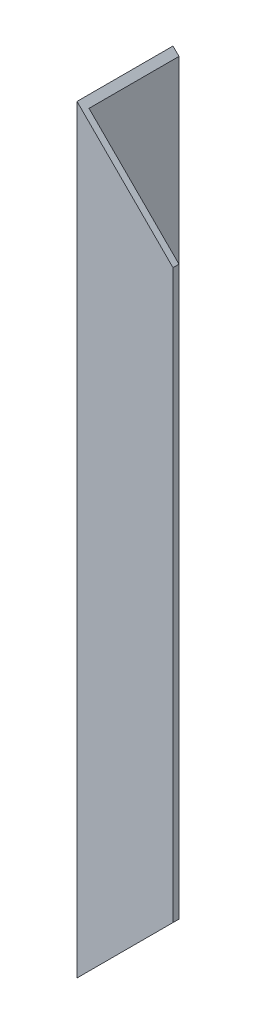
SolidWorks part; units mm, degrees
ref_plane "Front Plane" through (0, 0, 0) normal (0, 0, 1) x (1, 0, 0)
ref_plane "Top Plane" through (0, 0, 0) normal (0, 1, 0) x (1, 0, 0)
ref_plane "Right Plane" through (0, 0, 0) normal (1, 0, 0) x (0, 0, -1)
sketch "Sketch2" plane through (0, 0, 0) normal (0, 1, 0) x (1, 0, 0)
  line L0 (0, 0) -> (0, 25.4)
  line L1 (0, 25.4) -> (1.5875, 25.4)
  line L2 (1.5875, 25.4) -> (1.5875, 1.5875)
  line L3 (1.5875, 1.5875) -> (25.4, 1.5875)
  line L4 (25.4, 1.5875) -> (25.4, 0)
  line L5 (25.4, 0) -> (0, 0)
  dimension "D1" = 25.4
  dimension "D2" = 1.5875
extrude "Boss-Extrude2" add sketch "Sketch2" along normal blind 200.914
sketch "Sketch4" plane through (0, 0, 0) normal (0, 0, 1) x (1, 0, 0)
  line L0 (0, 200.914) -> (25.4, 175.514)
  line L1 (25.4, 200.914) -> (25.4, 0) construction
  line L2 (25.4, 175.514) -> (25.4, 200.914)
  line L3 (25.4, 200.914) -> (0, 200.914)
  dimension "D1" = 45
extrude "Cut-Extrude1" cut sketch "Sketch4" against normal through all
sketch "Sketch5" plane through (0, 0, 0) normal (0, 0, 1) x (1, 0, 0)
  line L0 (0, 0) -> (25.4, 25.4)
  line L1 (25.4, 175.514) -> (25.4, 0) construction
  line L2 (25.4, 25.4) -> (25.4, 0)
  line L3 (25.4, 0) -> (0, 0)
  dimension "D1" = 45
extrude "Cut-Extrude2" cut sketch "Sketch5" against normal through all
